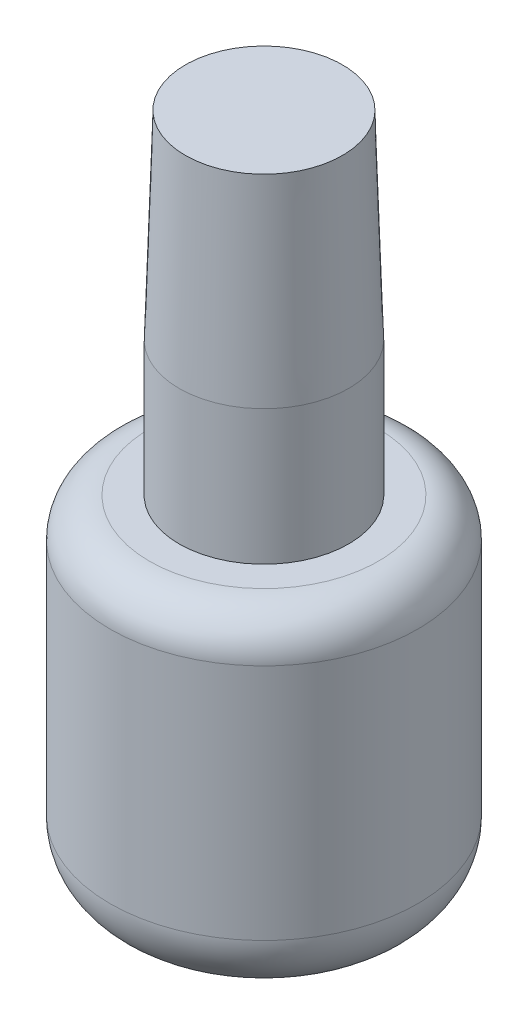
SolidWorks part; units mm, degrees
ref_plane "Front Plane" through (0, 0, 0) normal (0, 0, 1) x (1, 0, 0)
ref_plane "Top Plane" through (0, 0, 0) normal (0, 1, 0) x (1, 0, 0)
ref_plane "Right Plane" through (0, 0, 0) normal (1, 0, 0) x (0, 0, -1)
sketch "Sketch1" plane through (0, 0, 0) normal (0, 0, 1) x (1, 0, 0)
  line L0 (0, 0) -> (0, 15.9831) construction
  line L1 (0, 0) -> (-15.2731, 0) construction
  line L2 (12.446, 7.5567) -> (12.446, 26.797)
  line L3 (9.271, 29.972) -> (6.858, 29.972)
  line L4 (6.858, 29.972) -> (6.858, 40.8686)
  line L5 (6.858, 40.8686) -> (6.3555, 56.9468)
  line L6 (6.3555, 56.9468) -> (0, 56.9468)
  line L7 (0, 56.9468) -> (0, 0)
  arc A0 (0, 0) -> (10.4352, 3.5087) centre (0, 17.272) ccw
  arc A1 (10.4352, 3.5087) -> (12.446, 7.5567) centre (7.366, 7.5567) ccw
  arc A2 (12.446, 26.797) -> (9.271, 29.972) centre (9.271, 26.797) ccw
  dimension "D1" = 17.272
  dimension "D2" = 5.08
  dimension "D3" = 3.175
  dimension "D4" = 29.972
  dimension "D5" = 6.858
  dimension "D6" = 10.8966
  dimension "D7" = 12.446
  dimension "D8" = 1.79
  dimension "D9" = 56.9468
revolve "Revolve1" add sketch "Sketch1" angle 360 about L7
